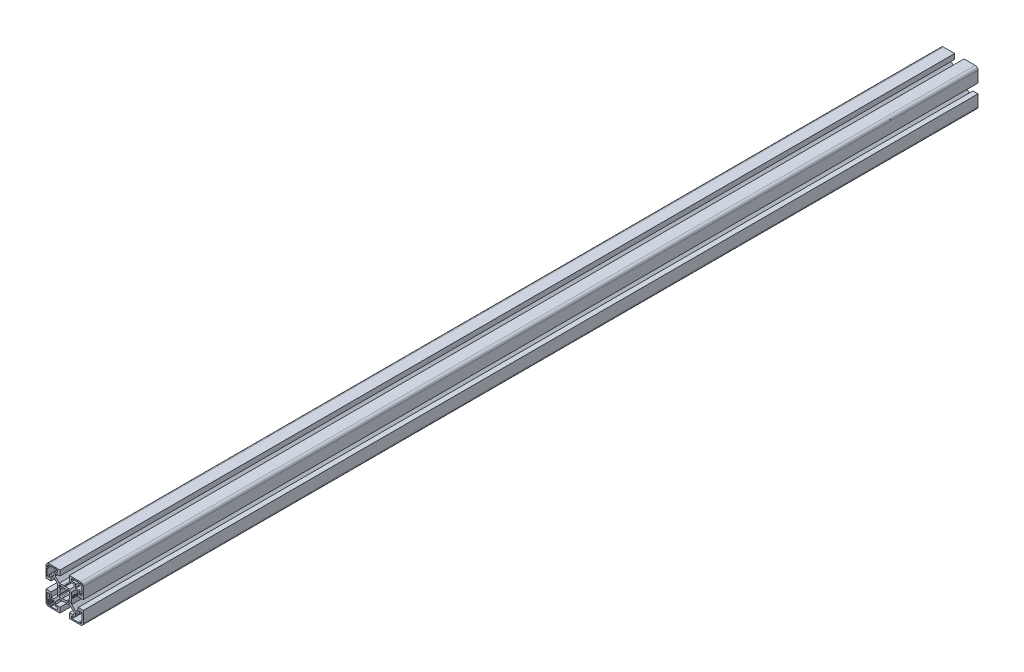
SolidWorks part; units mm, degrees
ref_plane "Front Plane" through (0, 0, 0) normal (0, 0, 1) x (1, 0, 0)
ref_plane "Top Plane" through (0, 0, 0) normal (0, 1, 0) x (1, 0, 0)
ref_plane "Right Plane" through (0, 0, 0) normal (1, 0, 0) x (0, 0, -1)
sketch "Sketch1" plane through (0, 0, 0) normal (0, 0, 1) x (1, 0, 0)
  line L0 (-11.7678, -10) -> (-14.5, -10)
  line L1 (-14.5, -10) -> (-14.5, -5)
  line L2 (-14.5, -5) -> (-20, -5)
  line L3 (-20, -5) -> (-20, -17)
  line L4 (-17, -20) -> (-5, -20)
  line L5 (-5, -20) -> (-5, -14.5)
  line L6 (-5, -14.5) -> (-10, -14.5)
  line L7 (-10, -14.5) -> (-10, -11.7678)
  line L8 (-10, -11.7678) -> (-5.7322, -7.5)
  line L9 (-5.7322, -7.5) -> (-0.6536, -7.5)
  line L10 (-0.4036, -7.433) -> (0, -7.2)
  line L11 (0, -7.2) -> (0.4036, -7.433)
  line L12 (0.9036, -7.433) -> (1.2189, -7.251)
  line L13 (1.2189, -7.251) -> (2.5, -7.5)
  line L14 (2.5, -7.5) -> (5.7322, -7.5)
  line L15 (5.7322, -7.5) -> (10, -11.7678)
  line L16 (10, -11.7678) -> (10, -14.5)
  line L17 (10, -14.5) -> (5, -14.5)
  line L18 (5, -14.5) -> (5, -20)
  line L19 (5, -20) -> (17, -20)
  line L20 (20, -17) -> (20, -5)
  line L21 (20, -5) -> (14.5, -5)
  line L22 (14.5, -5) -> (14.5, -10)
  line L23 (14.5, -10) -> (11.7678, -10)
  line L24 (11.7678, -10) -> (7.5, -5.7322)
  line L25 (7.5, -5.7322) -> (7.5, -0.6536)
  line L26 (7.433, -0.4036) -> (7.2, 0)
  line L27 (7.2, 0) -> (7.433, 0.4036)
  line L28 (7.433, 0.9036) -> (7.251, 1.2189)
  line L29 (7.251, 1.2189) -> (7.5, 2.5)
  line L30 (7.5, 2.5) -> (7.5, 5.7322)
  line L31 (7.5, 5.7322) -> (11.7678, 10)
  line L32 (11.7678, 10) -> (14.5, 10)
  line L33 (14.5, 10) -> (14.5, 5)
  line L34 (14.5, 5) -> (20, 5)
  line L35 (20, 5) -> (20, 17)
  line L36 (17, 20) -> (5, 20)
  line L37 (5, 20) -> (5, 14.5)
  line L38 (5, 14.5) -> (10, 14.5)
  line L39 (10, 14.5) -> (10, 11.7678)
  line L40 (10, 11.7678) -> (5.7322, 7.5)
  line L41 (5.7322, 7.5) -> (0.6536, 7.5)
  line L42 (0.4036, 7.433) -> (0, 7.2)
  line L43 (0, 7.2) -> (-0.4036, 7.433)
  line L44 (-0.9036, 7.433) -> (-1.2189, 7.251)
  line L45 (-1.2189, 7.251) -> (-2.5, 7.5)
  line L46 (-2.5, 7.5) -> (-5.7322, 7.5)
  line L47 (-5.7322, 7.5) -> (-10, 11.7678)
  line L48 (-10, 11.7678) -> (-10, 14.5)
  line L49 (-10, 14.5) -> (-5, 14.5)
  line L50 (-5, 14.5) -> (-5, 20)
  line L51 (-5, 20) -> (-17, 20)
  line L52 (-20, 17) -> (-20, 5)
  line L53 (-20, 5) -> (-14.5, 5)
  line L54 (-14.5, 5) -> (-14.5, 10)
  line L55 (-14.5, 10) -> (-11.7678, 10)
  line L56 (-11.7678, 10) -> (-7.5, 5.7322)
  line L57 (-7.5, 5.7322) -> (-7.5, 0.6536)
  line L58 (-7.433, 0.4036) -> (-7.2, 0)
  line L59 (-7.2, 0) -> (-7.433, -0.4036)
  line L60 (-7.433, -0.9036) -> (-7.251, -1.2189)
  line L61 (-7.251, -1.2189) -> (-7.5, -2.5)
  line L62 (-7.5, -2.5) -> (-7.5, -5.7322)
  line L63 (-7.5, -5.7322) -> (-11.7678, -10)
  line L64 (7.5, 16.5) -> (7.5, 18.2)
  line L65 (8, 18.7) -> (14.8, 18.7)
  line L66 (15, 18.5) -> (15, 18.2)
  line L67 (15.2, 18) -> (16.4, 18)
  line L68 (16.6, 18.2) -> (16.6, 18.5)
  line L69 (16.8, 18.7) -> (17.3, 18.7)
  line L70 (17.6, 18.4) -> (17.6, 17.9)
  line L71 (17.9, 17.6) -> (18.4, 17.6)
  line L72 (18.7, 17.3) -> (18.7, 16.8)
  line L73 (18.5, 16.6) -> (18.2, 16.6)
  line L74 (18, 16.4) -> (18, 15.2)
  line L75 (18.2, 15) -> (18.5, 15)
  line L76 (18.7, 14.8) -> (18.7, 8)
  line L77 (18.2, 7.5) -> (16.5, 7.5)
  line L78 (16, 8) -> (16, 10.2)
  line L79 (14.7, 11.5) -> (12, 11.5)
  line L80 (11.5, 12) -> (11.5, 14.7)
  line L81 (10.2, 16) -> (8, 16)
  line L82 (14.8, -18.7) -> (8, -18.7)
  line L83 (7.5, -18.2) -> (7.5, -16.5)
  line L84 (8, -16) -> (10.2, -16)
  line L85 (11.5, -14.7) -> (11.5, -12)
  line L86 (12, -11.5) -> (14.7, -11.5)
  line L87 (16, -10.2) -> (16, -8)
  line L88 (16.5, -7.5) -> (18.2, -7.5)
  line L89 (18.7, -8) -> (18.7, -14.8)
  line L90 (18.5, -15) -> (18.2, -15)
  line L91 (18, -15.2) -> (18, -16.4)
  line L92 (18.2, -16.6) -> (18.5, -16.6)
  line L93 (18.7, -16.8) -> (18.7, -17.3)
  line L94 (18.4, -17.6) -> (17.9, -17.6)
  line L95 (17.6, -17.9) -> (17.6, -18.4)
  line L96 (17.3, -18.7) -> (16.8, -18.7)
  line L97 (16.6, -18.5) -> (16.6, -18.2)
  line L98 (16.4, -18) -> (15.2, -18)
  line L99 (15, -18.2) -> (15, -18.5)
  line L100 (-18.7, 16.8) -> (-18.7, 17.3)
  line L101 (-18.4, 17.6) -> (-17.9, 17.6)
  line L102 (-17.6, 17.9) -> (-17.6, 18.4)
  line L103 (-17.3, 18.7) -> (-16.8, 18.7)
  line L104 (-16.6, 18.5) -> (-16.6, 18.2)
  line L105 (-16.4, 18) -> (-15.2, 18)
  line L106 (-15, 18.2) -> (-15, 18.5)
  line L107 (-14.8, 18.7) -> (-8, 18.7)
  line L108 (-7.5, 18.2) -> (-7.5, 16.5)
  line L109 (-8, 16) -> (-10.2, 16)
  line L110 (-11.5, 14.7) -> (-11.5, 12)
  line L111 (-12, 11.5) -> (-14.7, 11.5)
  line L112 (-16, 10.2) -> (-16, 8)
  line L113 (-16.5, 7.5) -> (-18.2, 7.5)
  line L114 (-18.7, 8) -> (-18.7, 14.8)
  line L115 (-18.5, 15) -> (-18.2, 15)
  line L116 (-18, 15.2) -> (-18, 16.4)
  line L117 (-18.2, 16.6) -> (-18.5, 16.6)
  line L118 (-18.7, -14.8) -> (-18.7, -8)
  line L119 (-18.2, -7.5) -> (-16.5, -7.5)
  line L120 (-16, -8) -> (-16, -10.2)
  line L121 (-14.7, -11.5) -> (-12, -11.5)
  line L122 (-11.5, -12) -> (-11.5, -14.7)
  line L123 (-10.2, -16) -> (-8, -16)
  line L124 (-7.5, -16.5) -> (-7.5, -18.2)
  line L125 (-8, -18.7) -> (-14.8, -18.7)
  line L126 (-15, -18.5) -> (-15, -18.2)
  line L127 (-15.2, -18) -> (-16.4, -18)
  line L128 (-16.6, -18.2) -> (-16.6, -18.5)
  line L129 (-16.8, -18.7) -> (-17.3, -18.7)
  line L130 (-17.6, -18.4) -> (-17.6, -17.9)
  line L131 (-17.9, -17.6) -> (-18.4, -17.6)
  line L132 (-18.7, -17.3) -> (-18.7, -16.8)
  line L133 (-18.5, -16.6) -> (-18.2, -16.6)
  line L134 (-18, -16.4) -> (-18, -15.2)
  line L135 (-18.2, -15) -> (-18.5, -15)
  line L136 (-6, 3.4907) -> (-6, 5)
  line L137 (-5, 6) -> (-3.4907, 6)
  line L138 (-3.0492, 5.7347) -> (-2.6892, 5.0577)
  line L139 (2.6892, 5.0577) -> (3.0492, 5.7347)
  line L140 (3.4907, 6) -> (5, 6)
  line L141 (6, 5) -> (6, 3.4907)
  line L142 (5.7347, 3.0492) -> (5.0577, 2.6892)
  line L143 (5.0577, -2.6892) -> (5.7347, -3.0492)
  line L144 (6, -3.4907) -> (6, -5)
  line L145 (5, -6) -> (3.4907, -6)
  line L146 (3.0492, -5.7347) -> (2.6892, -5.0577)
  line L147 (-2.6892, -5.0577) -> (-3.0492, -5.7347)
  line L148 (-3.4907, -6) -> (-5, -6)
  line L149 (-6, -5) -> (-6, -3.4907)
  line L150 (-5.7347, -3.0492) -> (-5.0577, -2.6892)
  line L151 (-5.0577, 2.6892) -> (-5.7347, 3.0492)
  arc A0 (-20, -17) -> (-17, -20) centre (-17, -17) ccw
  arc A1 (-0.6536, -7.5) -> (-0.4036, -7.433) centre (-0.6536, -7) ccw
  arc A2 (0.4036, -7.433) -> (0.9036, -7.433) centre (0.6536, -7) ccw
  arc A3 (17, -20) -> (20, -17) centre (17, -17) ccw
  arc A4 (7.5, -0.6536) -> (7.433, -0.4036) centre (7, -0.6536) ccw
  arc A5 (7.433, 0.4036) -> (7.433, 0.9036) centre (7, 0.6536) ccw
  arc A6 (20, 17) -> (17, 20) centre (17, 17) ccw
  arc A7 (0.6536, 7.5) -> (0.4036, 7.433) centre (0.6536, 7) ccw
  arc A8 (-0.4036, 7.433) -> (-0.9036, 7.433) centre (-0.6536, 7) ccw
  arc A9 (-17, 20) -> (-20, 17) centre (-17, 17) ccw
  arc A10 (-7.5, 0.6536) -> (-7.433, 0.4036) centre (-7, 0.6536) ccw
  arc A11 (-7.433, -0.4036) -> (-7.433, -0.9036) centre (-7, -0.6536) ccw
  arc A12 (8, 16) -> (7.5, 16.5) centre (8, 16.5) cw
  arc A13 (7.5, 18.2) -> (8, 18.7) centre (8, 18.2) cw
  arc A14 (14.8, 18.7) -> (15, 18.5) centre (14.8, 18.5) cw
  arc A15 (15, 18.2) -> (15.2, 18) centre (15.2, 18.2) ccw
  arc A16 (16.4, 18) -> (16.6, 18.2) centre (16.4, 18.2) ccw
  arc A17 (16.6, 18.5) -> (16.8, 18.7) centre (16.8, 18.5) cw
  arc A18 (17.3, 18.7) -> (17.6, 18.4) centre (17.3, 18.4) cw
  arc A19 (17.6, 17.9) -> (17.9, 17.6) centre (17.9, 17.9) ccw
  arc A20 (18.4, 17.6) -> (18.7, 17.3) centre (18.4, 17.3) cw
  arc A21 (18.7, 16.8) -> (18.5, 16.6) centre (18.5, 16.8) cw
  arc A22 (18.2, 16.6) -> (18, 16.4) centre (18.2, 16.4) ccw
  arc A23 (18, 15.2) -> (18.2, 15) centre (18.2, 15.2) ccw
  arc A24 (18.5, 15) -> (18.7, 14.8) centre (18.5, 14.8) cw
  arc A25 (18.7, 8) -> (18.2, 7.5) centre (18.2, 8) cw
  arc A26 (16.5, 7.5) -> (16, 8) centre (16.5, 8) cw
  arc A27 (16, 10.2) -> (14.7, 11.5) centre (14.7, 10.2) ccw
  arc A28 (12, 11.5) -> (11.5, 12) centre (12, 12) cw
  arc A29 (11.5, 14.7) -> (10.2, 16) centre (10.2, 14.7) ccw
  arc A30 (8, -18.7) -> (7.5, -18.2) centre (8, -18.2) cw
  arc A31 (7.5, -16.5) -> (8, -16) centre (8, -16.5) cw
  arc A32 (10.2, -16) -> (11.5, -14.7) centre (10.2, -14.7) ccw
  arc A33 (11.5, -12) -> (12, -11.5) centre (12, -12) cw
  arc A34 (14.7, -11.5) -> (16, -10.2) centre (14.7, -10.2) ccw
  arc A35 (16, -8) -> (16.5, -7.5) centre (16.5, -8) cw
  arc A36 (18.2, -7.5) -> (18.7, -8) centre (18.2, -8) cw
  arc A37 (18.7, -14.8) -> (18.5, -15) centre (18.5, -14.8) cw
  arc A38 (18.2, -15) -> (18, -15.2) centre (18.2, -15.2) ccw
  arc A39 (18, -16.4) -> (18.2, -16.6) centre (18.2, -16.4) ccw
  arc A40 (18.5, -16.6) -> (18.7, -16.8) centre (18.5, -16.8) cw
  arc A41 (18.7, -17.3) -> (18.4, -17.6) centre (18.4, -17.3) cw
  arc A42 (17.9, -17.6) -> (17.6, -17.9) centre (17.9, -17.9) ccw
  arc A43 (17.6, -18.4) -> (17.3, -18.7) centre (17.3, -18.4) cw
  arc A44 (16.8, -18.7) -> (16.6, -18.5) centre (16.8, -18.5) cw
  arc A45 (16.6, -18.2) -> (16.4, -18) centre (16.4, -18.2) ccw
  arc A46 (15.2, -18) -> (15, -18.2) centre (15.2, -18.2) ccw
  arc A47 (15, -18.5) -> (14.8, -18.7) centre (14.8, -18.5) cw
  arc A48 (-18.5, 16.6) -> (-18.7, 16.8) centre (-18.5, 16.8) cw
  arc A49 (-18.7, 17.3) -> (-18.4, 17.6) centre (-18.4, 17.3) cw
  arc A50 (-17.9, 17.6) -> (-17.6, 17.9) centre (-17.9, 17.9) ccw
  arc A51 (-17.6, 18.4) -> (-17.3, 18.7) centre (-17.3, 18.4) cw
  arc A52 (-16.8, 18.7) -> (-16.6, 18.5) centre (-16.8, 18.5) cw
  arc A53 (-16.6, 18.2) -> (-16.4, 18) centre (-16.4, 18.2) ccw
  arc A54 (-15.2, 18) -> (-15, 18.2) centre (-15.2, 18.2) ccw
  arc A55 (-15, 18.5) -> (-14.8, 18.7) centre (-14.8, 18.5) cw
  arc A56 (-8, 18.7) -> (-7.5, 18.2) centre (-8, 18.2) cw
  arc A57 (-7.5, 16.5) -> (-8, 16) centre (-8, 16.5) cw
  arc A58 (-10.2, 16) -> (-11.5, 14.7) centre (-10.2, 14.7) ccw
  arc A59 (-11.5, 12) -> (-12, 11.5) centre (-12, 12) cw
  arc A60 (-14.7, 11.5) -> (-16, 10.2) centre (-14.7, 10.2) ccw
  arc A61 (-16, 8) -> (-16.5, 7.5) centre (-16.5, 8) cw
  arc A62 (-18.2, 7.5) -> (-18.7, 8) centre (-18.2, 8) cw
  arc A63 (-18.7, 14.8) -> (-18.5, 15) centre (-18.5, 14.8) cw
  arc A64 (-18.2, 15) -> (-18, 15.2) centre (-18.2, 15.2) ccw
  arc A65 (-18, 16.4) -> (-18.2, 16.6) centre (-18.2, 16.4) ccw
  arc A66 (-18.5, -15) -> (-18.7, -14.8) centre (-18.5, -14.8) cw
  arc A67 (-18.7, -8) -> (-18.2, -7.5) centre (-18.2, -8) cw
  arc A68 (-16.5, -7.5) -> (-16, -8) centre (-16.5, -8) cw
  arc A69 (-16, -10.2) -> (-14.7, -11.5) centre (-14.7, -10.2) ccw
  arc A70 (-12, -11.5) -> (-11.5, -12) centre (-12, -12) cw
  arc A71 (-11.5, -14.7) -> (-10.2, -16) centre (-10.2, -14.7) ccw
  arc A72 (-8, -16) -> (-7.5, -16.5) centre (-8, -16.5) cw
  arc A73 (-7.5, -18.2) -> (-8, -18.7) centre (-8, -18.2) cw
  arc A74 (-14.8, -18.7) -> (-15, -18.5) centre (-14.8, -18.5) cw
  arc A75 (-15, -18.2) -> (-15.2, -18) centre (-15.2, -18.2) ccw
  arc A76 (-16.4, -18) -> (-16.6, -18.2) centre (-16.4, -18.2) ccw
  arc A77 (-16.6, -18.5) -> (-16.8, -18.7) centre (-16.8, -18.5) cw
  arc A78 (-17.3, -18.7) -> (-17.6, -18.4) centre (-17.3, -18.4) cw
  arc A79 (-17.6, -17.9) -> (-17.9, -17.6) centre (-17.9, -17.9) ccw
  arc A80 (-18.4, -17.6) -> (-18.7, -17.3) centre (-18.4, -17.3) cw
  arc A81 (-18.7, -16.8) -> (-18.5, -16.6) centre (-18.5, -16.8) cw
  arc A82 (-18.2, -16.6) -> (-18, -16.4) centre (-18.2, -16.4) ccw
  arc A83 (-18, -15.2) -> (-18.2, -15) centre (-18.2, -15.2) ccw
  arc A84 (-5.7347, 3.0492) -> (-6, 3.4907) centre (-5.5, 3.4907) cw
  arc A85 (-6, 5) -> (-5, 6) centre (-5, 5) cw
  arc A86 (-3.4907, 6) -> (-3.0492, 5.7347) centre (-3.4907, 5.5) cw
  arc A87 (-2.6892, 5.0577) -> (-2.0523, 4.8322) centre (-2.2478, 5.2925) ccw
  arc A88 (-2.0523, 4.8322) -> (2.0523, 4.8322) centre (0, 0) cw
  arc A89 (2.0523, 4.8322) -> (2.6892, 5.0577) centre (2.2478, 5.2925) ccw
  arc A90 (3.0492, 5.7347) -> (3.4907, 6) centre (3.4907, 5.5) cw
  arc A91 (5, 6) -> (6, 5) centre (5, 5) cw
  arc A92 (6, 3.4907) -> (5.7347, 3.0492) centre (5.5, 3.4907) cw
  arc A93 (5.0577, 2.6892) -> (4.8322, 2.0523) centre (5.2925, 2.2478) ccw
  arc A94 (4.8322, 2.0523) -> (4.8322, -2.0523) centre (0, 0) cw
  arc A95 (4.8322, -2.0523) -> (5.0577, -2.6892) centre (5.2925, -2.2478) ccw
  arc A96 (5.7347, -3.0492) -> (6, -3.4907) centre (5.5, -3.4907) cw
  arc A97 (6, -5) -> (5, -6) centre (5, -5) cw
  arc A98 (3.4907, -6) -> (3.0492, -5.7347) centre (3.4907, -5.5) cw
  arc A99 (2.6892, -5.0577) -> (2.0523, -4.8322) centre (2.2478, -5.2925) ccw
  arc A100 (2.0523, -4.8322) -> (-2.0523, -4.8322) centre (0, 0) cw
  arc A101 (-2.0523, -4.8322) -> (-2.6892, -5.0577) centre (-2.2478, -5.2925) ccw
  arc A102 (-3.0492, -5.7347) -> (-3.4907, -6) centre (-3.4907, -5.5) cw
  arc A103 (-5, -6) -> (-6, -5) centre (-5, -5) cw
  arc A104 (-6, -3.4907) -> (-5.7347, -3.0492) centre (-5.5, -3.4907) cw
  arc A105 (-5.0577, -2.6892) -> (-4.8322, -2.0523) centre (-5.2925, -2.2478) ccw
  arc A106 (-4.8322, -2.0523) -> (-4.8322, 2.0523) centre (0, 0) cw
  arc A107 (-4.8322, 2.0523) -> (-5.0577, 2.6892) centre (-5.2925, 2.2478) ccw
extrude "Boss-Extrude1" add sketch "Sketch1" against normal blind 960
